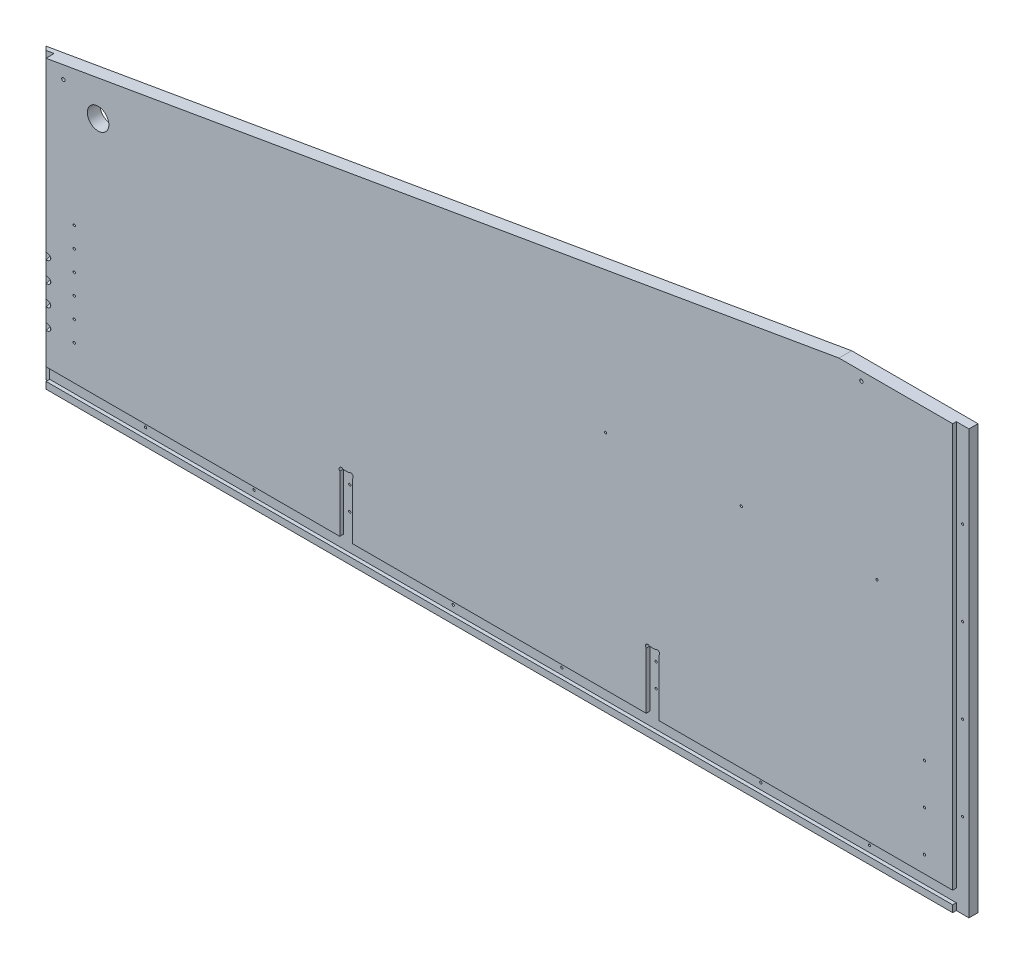
SolidWorks part; units mm, degrees
material "Maple"
ref_plane "Front Plane" through (0, 0, 0) normal (0, 0, 1) x (1, 0, 0)
ref_plane "Top Plane" through (0, 0, 0) normal (0, 1, 0) x (1, 0, 0)
ref_plane "Right Plane" through (0, 0, 0) normal (1, 0, 0) x (0, 0, -1)
sketch "Sketch1" plane through (0, 0, 0) normal (0, 0, 1) x (1, 0, 0)
  line L0 (8932.6508, -5243.5125) -> (10226.1458, -5243.5125)
  line L1 (9086.3208, -4722.0918) -> (10222.9708, -4853.7812)
  line L2 (8914.8708, -6342.0625) -> (10197.5708, -6342.0625)
  line L3 (8914.8708, -5808.6625) -> (10197.5708, -5808.6625)
  line L4 (8919.6333, -5253.0375) -> (10218.2083, -5253.0375)
  line L5 (9134.2633, -4656.1375) -> (9134.2633, -4638.3575)
  line L6 (9091.0833, -4638.3575) -> (9134.2633, -4638.3575)
  line L7 (9091.0833, -4567.2375) -> (9091.0833, -4638.3575)
  line L8 (9134.2633, -4656.1375) -> (9581.3033, -4656.1375)
  line L9 (9091.0833, -4567.2375) -> (9624.4833, -4567.2375)
  line L10 (9581.3033, -4656.1375) -> (9581.3033, -4638.3575)
  line L11 (9581.3033, -4638.3575) -> (9624.4833, -4638.3575)
  line L12 (9624.4833, -4567.2375) -> (9624.4833, -4638.3575)
  line L13 (8932.6508, -5225.7325) -> (9344.9775, -5225.7325)
  line L14 (8932.6508, -5256.2125) -> (8932.6508, -5243.5125)
  line L15 (8911.6958, -5256.2125) -> (8932.6508, -5256.2125)
  line L16 (8914.8708, -4722.0918) -> (9086.3208, -4722.0918)
  line L17 (8911.6958, -4715.5913) -> (8932.6508, -4715.5913)
  line L18 (8914.8708, -6342.0625) -> (8914.8708, -5808.6625)
  line L19 (12082.9917, -4722.0918) -> (10946.3417, -4853.7812)
  line L20 (12236.6617, -5243.5125) -> (10943.1667, -5243.5125)
  line L21 (10951.1042, -5253.0375) -> (12249.6792, -5253.0375)
  line L22 (10838.3917, -5656.2625) -> (11308.2917, -5656.2625)
  line L23 (10838.3917, -5719.7625) -> (11308.2917, -5719.7625)
  line L24 (10838.3917, -5742.5368) -> (11308.2917, -5742.5368)
  line L25 (10806.6417, -6342.0625) -> (11340.0417, -6342.0625)
  line L26 (10803.4667, -6335.7125) -> (11343.2167, -6335.7125)
  line L27 (10803.4667, -6317.9325) -> (11343.2167, -6317.9325)
  line L28 (10943.1667, -5225.7325) -> (11376.4483, -5225.7325)
  line L29 (11506.7292, -4754.5625) -> (10806.6417, -4827.5875)
  line L30 (11506.7292, -4567.2375) -> (11506.7292, -4754.5625)
  line L31 (10806.6417, -4567.2375) -> (10806.6417, -4827.5875)
  line L32 (10806.6417, -4567.2375) -> (11506.7292, -4567.2375)
  line L33 (10235.6708, -6329.3625) -> (10245.1958, -6329.3625)
  line L34 (10245.1958, -6329.3625) -> (10254.7208, -6278.5625)
  line L35 (10302.3458, -6329.3625) -> (10311.8708, -6278.5625)
  line L36 (10302.3458, -6329.3625) -> (10292.8208, -6329.3625)
  line L37 (10245.1958, -5821.3625) -> (10254.7208, -5872.1625)
  line L38 (10235.6708, -5821.3625) -> (10245.1958, -5821.3625)
  line L39 (10292.8208, -5821.3625) -> (10302.3458, -5821.3625)
  line L40 (10302.3458, -5821.3625) -> (10311.8708, -5872.1625)
  line L41 (10235.6708, -5821.3625) -> (10235.6708, -6329.3625)
  line L42 (10254.7208, -5872.1625) -> (10254.7208, -6278.5625)
  line L43 (10311.8708, -5872.1625) -> (10311.8708, -6278.5625)
  line L44 (10292.8208, -5821.3625) -> (10292.8208, -6329.3625)
  line L45 (8932.6508, -5225.7325) -> (8932.6508, -4715.5913)
  line L46 (8911.6958, -4715.5913) -> (8911.6958, -5256.2125)
  line L47 (8914.8708, -5248.275) -> (8914.8708, -4722.0918)
  line L48 (8919.6333, -5253.0375) -> (8914.8708, -5248.275)
  line L49 (8914.8708, -5145.0875) -> (8937.426, -5145.0875)
  line L50 (8914.8708, -5202.2375) -> (8937.426, -5202.2375)
  line L51 (10838.3917, -5656.2625) -> (10838.3917, -5719.7625)
  line L52 (10832.0417, -5736.1868) -> (10856.1717, -5736.1868)
  line L53 (10806.6417, -6342.0625) -> (10806.6417, -5818.7368)
  line L54 (10832.0417, -5649.9125) -> (10856.1717, -5649.9125)
  line L55 (10832.0417, -5726.1125) -> (10856.1717, -5726.1125)
  line L56 (10806.6417, -5818.7368) -> (10833.9015, -5818.7368)
  line L57 (10832.0417, -5806.0442) -> (10851.6815, -5806.0442)
  line L58 (10856.1717, -5801.5541) -> (10856.1717, -5736.1868)
  line L59 (10838.3917, -5814.2467) -> (10838.3917, -5742.5368)
  line L60 (10832.0417, -5806.0442) -> (10832.0417, -5736.1868)
  line L61 (10803.4667, -6317.9325) -> (10803.4667, -6335.7125)
  line L62 (10197.5708, -5808.6625) -> (10197.5708, -6342.0625)
  line L63 (9762.3842, -6348.4125) -> (9762.3842, -5802.3125)
  line L64 (9780.1642, -6348.4125) -> (9762.3842, -6348.4125)
  line L65 (9780.1642, -5802.3125) -> (9780.1642, -6348.4125)
  line L66 (9762.3842, -5802.3125) -> (9780.1642, -5802.3125)
  line L67 (9332.2775, -6348.4125) -> (9332.2775, -5802.3125)
  line L68 (9332.2775, -6348.4125) -> (9350.0575, -6348.4125)
  line L69 (9350.0575, -5802.3125) -> (9350.0575, -6348.4125)
  line L70 (9332.2775, -5802.3125) -> (9350.0575, -5802.3125)
  line L71 (9993.8374, -6061.075) -> (9993.8374, -6045.2418)
  line L72 (9998.5999, -6065.8375) -> (10014.4331, -6065.8375)
  line L73 (9998.5999, -6084.8875) -> (10014.4331, -6084.8875)
  line L74 (9993.8374, -6105.4832) -> (9993.8374, -6089.65)
  line L75 (9974.7874, -6105.4832) -> (9974.7874, -6089.65)
  line L76 (9954.1917, -6084.8875) -> (9970.0249, -6084.8875)
  line L77 (9974.7874, -6061.075) -> (9974.7874, -6045.2418)
  line L78 (9954.1917, -6065.8375) -> (9970.0249, -6065.8375)
  line L79 (10793.9417, -6237.2875) -> (10816.4969, -6237.2875)
  line L80 (10793.9417, -6294.4375) -> (10816.4969, -6294.4375)
  line L81 (10856.1717, -5649.9125) -> (10856.1717, -5726.1125)
  line L82 (10832.0417, -5726.1125) -> (10832.0417, -5649.9125)
  line L83 (10226.1458, -5225.7325) -> (10226.1458, -5243.5125)
  line L84 (10205.1908, -5257.8) -> (10205.1908, -4844.2499)
  line L85 (10230.9083, -4844.2499) -> (10230.9083, -5257.8)
  line L86 (10205.1908, -5257.8) -> (10230.9083, -5257.8)
  line L87 (10205.1908, -4844.2499) -> (10230.9083, -4844.2499)
  line L88 (10946.3417, -5176.8375) -> (10968.8969, -5176.8375)
  line L89 (9349.4676, -5141.9125) -> (9358.2674, -5141.9125)
  line L90 (10946.3417, -5119.6875) -> (10968.8969, -5119.6875)
  line L91 (9929.011, -4660.9635) -> (10066.0807, -4660.9635)
  line L92 (9929.011, -4678.7435) -> (10066.0807, -4678.7435)
  line L93 (10943.1667, -5225.7325) -> (10943.1667, -5243.5125)
  line L94 (10946.3417, -5248.275) -> (10951.1042, -5253.0375)
  line L95 (10946.3417, -5257.8063) -> (10946.3417, -4849.0188)
  line L96 (10964.1217, -5257.8) -> (10964.1217, -4844.2499)
  line L97 (10938.4042, -4844.2499) -> (10938.4042, -5257.8)
  line L98 (10938.4042, -5257.8) -> (10964.1217, -5257.8)
  line L99 (10964.1217, -4844.2499) -> (10938.4042, -4844.2499)
  line L100 (10344.8908, -4560.8875) -> (10369.0208, -4560.8875)
  line L101 (10344.8908, -4560.8875) -> (10369.0208, -4560.8875)
  line L102 (10800.2917, -4560.8875) -> (10824.4217, -4560.8875)
  line L103 (10200.4156, -5119.6875) -> (10222.9708, -5119.6875)
  line L104 (10200.4156, -5176.8375) -> (10222.9708, -5176.8375)
  line L105 (9344.9775, -5146.4026) -> (9344.9775, -5225.7325)
  line L106 (10344.8908, -4560.8875) -> (10344.8908, -4833.9375)
  line L107 (9792.8642, -5225.7325) -> (9792.8642, -5146.4026)
  line L108 (9362.7575, -5225.7325) -> (9775.0842, -5225.7325)
  line L109 (9680.3633, -4761.8396) -> (9680.3633, -4559.9604)
  line L110 (9656.2333, -4559.9604) -> (9680.3633, -4559.9604)
  line L111 (9656.2333, -4761.8396) -> (9680.3633, -4761.8396)
  line L112 (9656.2333, -4761.8396) -> (9656.2333, -4559.9604)
  line L113 (9779.5743, -5141.9125) -> (9788.374, -5141.9125)
  line L114 (10070.5708, -4665.4536) -> (10070.5708, -4674.2534)
  line L115 (9924.5208, -4674.2534) -> (9924.5208, -4665.4536)
  line L116 (12127.4417, -6188.3925) -> (12205.5015, -6188.3925)
  line L117 (12209.9917, -6170.6125) -> (12209.9917, -6183.9024)
  line L118 (9792.8642, -5225.7325) -> (10226.1458, -5225.7325)
  line L119 (9662.5833, -4754.5625) -> (10362.6708, -4827.5875)
  line L120 (9662.5833, -4567.2375) -> (9662.5833, -4754.5625)
  line L121 (10362.6708, -4567.2375) -> (10362.6708, -4827.5875)
  line L122 (9662.5833, -4567.2375) -> (10362.6708, -4567.2375)
  line L123 (10824.4217, -4833.9375) -> (10800.2917, -4833.9375)
  line L124 (10800.2917, -4833.9375) -> (10800.2917, -4560.8875)
  line L125 (10824.4217, -4560.8875) -> (10824.4217, -4833.9375)
  line L126 (10344.8908, -4833.9375) -> (10369.0208, -4833.9375)
  line L127 (10369.0208, -4833.9375) -> (10369.0208, -4560.8875)
  line L128 (10222.9708, -5248.275) -> (10218.2083, -5253.0375)
  line L129 (10222.9708, -5257.8063) -> (10222.9708, -4849.0188)
  line L130 (11734.6544, -5701.375) -> (11739.2301, -5701.375)
  line L131 (9362.7575, -5225.7325) -> (9362.7575, -5146.4026)
  line L132 (9775.0842, -5146.4026) -> (9775.0842, -5225.7325)
  line L133 (11761.3864, -5701.375) -> (11756.8282, -5701.375)
  line L134 (11734.6544, -5693.755) -> (11739.2301, -5693.755)
  line L135 (11761.4039, -5693.755) -> (11756.8282, -5693.755)
  line L136 (11734.6544, -5701.375) -> (11739.2301, -5701.375)
  line L137 (11744.3462, -5721.3024) -> (11744.3462, -5706.4179)
  line L138 (11751.7122, -5721.3024) -> (11751.7122, -5706.4179)
  line L139 (11740.0917, -6170.6125) -> (11740.0917, -6183.9024)
  line L140 (11689.2917, -6188.3925) -> (11822.6417, -6188.3925)
  line L141 (11689.2917, -6348.4093) -> (11689.2917, -6164.2657)
  line L142 (11689.2917, -6164.2657) -> (11746.4417, -6164.2657)
  line L143 (11746.4417, -6164.2657) -> (11746.4417, -6188.3925)
  line L144 (11689.2917, -6164.2657) -> (11746.4417, -6164.2657)
  line L145 (11340.0417, -5818.7368) -> (11340.0417, -6342.0625)
  line L146 (11290.5117, -5726.1125) -> (11314.6417, -5726.1125)
  line L147 (11290.5117, -5649.9125) -> (11290.5117, -5726.1125)
  line L148 (11340.0417, -5818.7368) -> (11312.7818, -5818.7368)
  line L149 (11314.6417, -5806.0442) -> (11295.0018, -5806.0442)
  line L150 (11290.5117, -5801.5541) -> (11290.5117, -5736.1868)
  line L151 (11308.2917, -5814.2467) -> (11308.2917, -5742.5368)
  line L152 (11314.6417, -5806.0442) -> (11314.6417, -5736.1868)
  line L153 (11290.5117, -5736.1868) -> (11314.6417, -5736.1868)
  line L154 (11848.0417, -6267.1325) -> (11962.3417, -6267.1325)
  line L155 (11962.3417, -6267.1325) -> (11962.3417, -6203.6325)
  line L156 (11343.2167, -6317.9325) -> (11343.2167, -6335.7125)
  line L157 (11365.4417, -5656.2625) -> (11365.4417, -5719.7625)
  line L158 (11365.4417, -5656.2625) -> (11479.7417, -5656.2625)
  line L159 (11778.1917, -6071.3937) -> (11802.3217, -6071.3937)
  line L160 (11314.6417, -5726.1125) -> (11314.6417, -5649.9125)
  line L161 (11314.6417, -5649.9125) -> (11290.5117, -5649.9125)
  line L162 (11308.2917, -5719.7625) -> (11308.2917, -5656.2625)
  line L163 (11689.2917, -6348.4093) -> (11713.4217, -6348.4093)
  line L164 (12203.6417, -6164.2657) -> (12260.7917, -6164.2657)
  line L165 (11713.4217, -6348.4093) -> (11713.4217, -6164.2657)
  line L166 (11695.6417, -6342.0625) -> (11695.6417, -6170.6125)
  line L167 (11695.6417, -6048.5337) -> (11699.4517, -6052.3437)
  line L168 (11822.6417, -6292.5325) -> (11822.6417, -6188.3925)
  line L169 (11695.6417, -6342.0625) -> (11695.6417, -6170.6125)
  line L170 (11848.0417, -6203.6325) -> (11962.3417, -6203.6325)
  line L171 (11848.0417, -6203.6325) -> (11848.0417, -6267.1325)
  line L172 (11987.7417, -6267.1325) -> (11987.7417, -6203.6325)
  line L173 (11784.5417, -6077.7437) -> (11784.5417, -6141.2438)
  line L174 (11517.8417, -5656.2625) -> (11632.1417, -5656.2625)
  line L175 (11632.1417, -5656.2625) -> (11632.1417, -5719.7625)
  line L176 (11632.1417, -5719.7625) -> (11517.8417, -5719.7625)
  line L177 (11517.8417, -5719.7625) -> (11517.8417, -5656.2625)
  line L178 (11692.4667, -6028.2137) -> (11692.4667, -6045.9937)
  line L179 (11695.6417, -5979.3188) -> (11718.1969, -5979.3188)
  line L180 (11695.6417, -5922.1687) -> (11718.1969, -5922.1687)
  line L181 (11821.0415, -5722.9375) -> (11821.0415, -5943.6)
  line L182 (11687.7042, -5651.5) -> (11701.9917, -5651.5)
  line L183 (11687.7042, -5651.5) -> (11687.7042, -6055.5251)
  line L184 (11687.7042, -6055.5251) -> (11701.9917, -6055.5251)
  line L185 (11701.9917, -6055.5251) -> (11701.9917, -5651.5)
  line L186 (11695.6417, -6055.2013) -> (11695.6417, -5649.595)
  line L187 (11695.6417, -5656.2625) -> (11695.6417, -6048.5337)
  line L188 (11695.6417, -6170.6125) -> (11740.0917, -6170.6125)
  line L189 (12203.6417, -6164.2657) -> (12203.6417, -6188.3925)
  line L190 (12254.4417, -6342.0625) -> (12254.4417, -6170.6125)
  line L191 (12129.0419, -5943.6) -> (12129.0419, -5722.9375)
  line L192 (12254.4417, -6048.5337) -> (12250.6317, -6052.3437)
  line L193 (12257.6167, -6045.9937) -> (12257.6167, -6028.2137)
  line L194 (12248.0917, -5651.5) -> (12262.3792, -5651.5)
  line L195 (12262.3792, -5651.5) -> (12262.3792, -6055.5251)
  line L196 (12262.3792, -6055.5251) -> (12248.0917, -6055.5251)
  line L197 (12248.0917, -6055.5251) -> (12248.0917, -5651.5)
  line L198 (12254.4417, -6141.2438) -> (12254.4417, -6077.7437)
  line L199 (12236.6617, -6164.2657) -> (12260.7917, -6164.2657)
  line L200 (12102.0417, -6267.1325) -> (11987.7417, -6267.1325)
  line L201 (11330.1865, -6237.2875) -> (11352.7417, -6237.2875)
  line L202 (11330.1865, -6294.4375) -> (11352.7417, -6294.4375)
  line L203 (11474.6617, -5851.8425) -> (11492.4417, -5851.8425)
  line L204 (11474.6617, -5808.6625) -> (11474.6617, -5851.8425)
  line L205 (11403.5417, -5808.6625) -> (11474.6617, -5808.6625)
  line L206 (11492.4417, -5851.8425) -> (11492.4417, -6298.8825)
  line L207 (11403.5417, -6342.0625) -> (11403.5417, -5808.6625)
  line L208 (11474.6617, -6298.8825) -> (11492.4417, -6298.8825)
  line L209 (11474.6617, -6342.0625) -> (11474.6617, -6298.8825)
  line L210 (11403.5417, -6342.0625) -> (11474.6617, -6342.0625)
  line L211 (11619.4417, -5851.8425) -> (11601.6617, -5851.8425)
  line L212 (11601.6617, -5808.6625) -> (11601.6617, -5851.8425)
  line L213 (11530.5417, -5808.6625) -> (11601.6617, -5808.6625)
  line L214 (11619.4417, -5851.8425) -> (11619.4417, -6298.8825)
  line L215 (11530.5417, -6342.0625) -> (11530.5417, -5808.6625)
  line L216 (11619.4417, -6298.8825) -> (11601.6617, -6298.8825)
  line L217 (11601.6617, -6342.0625) -> (11601.6617, -6298.8825)
  line L218 (11530.5417, -6342.0625) -> (11601.6617, -6342.0625)
  line L219 (11479.7417, -5719.7625) -> (11479.7417, -5656.2625)
  line L220 (11365.4417, -5719.7625) -> (11479.7417, -5719.7625)
  line L221 (11778.1917, -6147.5937) -> (11802.3217, -6147.5937)
  line L222 (11802.3217, -6071.3937) -> (11802.3217, -6147.5937)
  line L223 (11778.1917, -6147.5937) -> (11778.1917, -6071.3937)
  line L224 (12254.4417, -5922.1687) -> (12231.8865, -5922.1687)
  line L225 (12254.4417, -5979.3188) -> (12231.8865, -5979.3188)
  line L226 (12254.4417, -6055.2013) -> (12254.4417, -5649.595)
  line L227 (12254.4417, -6048.5337) -> (12254.4417, -5656.2625)
  line L228 (11841.6917, -5702.2873) -> (12108.3917, -5702.2873)
  line L229 (11822.6417, -6292.5325) -> (12127.4417, -6292.5325)
  line L230 (12127.4417, -6292.5325) -> (12127.4417, -6188.3925)
  line L231 (12254.4417, -6170.6125) -> (12209.9917, -6170.6125)
  line L232 (11695.6417, -6342.0625) -> (12254.4417, -6342.0625)
  line L233 (12236.6617, -6348.4093) -> (12260.7917, -6348.4093)
  line L234 (12260.7917, -6348.4093) -> (12260.7917, -6164.2657)
  line L235 (12236.6617, -6348.4093) -> (12236.6617, -6164.2657)
  line L236 (12102.0417, -6203.6325) -> (12102.0417, -6267.1325)
  line L237 (11987.7417, -6203.6325) -> (12102.0417, -6203.6325)
  line L238 (12236.6617, -6147.5937) -> (12236.6617, -6071.3937)
  line L239 (12203.6417, -6188.3925) -> (12260.7917, -6188.3925)
  line L240 (11098.7417, -4665.4536) -> (11098.7417, -4674.2534)
  line L241 (11394.2283, -5146.4026) -> (11394.2283, -5225.7325)
  line L242 (11376.4483, -5225.7325) -> (11376.4483, -5146.4026)
  line L243 (11394.2283, -5225.7325) -> (11806.555, -5225.7325)
  line L244 (11841.6917, -5964.2502) -> (12108.3917, -5964.2502)
  line L245 (12236.6617, -6147.5937) -> (12260.7917, -6147.5937)
  line L246 (12236.6617, -5256.2125) -> (12236.6617, -5243.5125)
  line L247 (12260.7917, -6147.5937) -> (12260.7917, -6071.3937)
  line L248 (12260.7917, -6071.3937) -> (12236.6617, -6071.3937)
  line L249 (12254.4417, -6077.7437) -> (11784.5417, -6077.7437)
  line L250 (11784.5417, -6141.2438) -> (12254.4417, -6141.2438)
  line L252 (12254.4417, -5656.2625) -> (11695.6417, -5656.2625)
  line L253 (11699.4517, -6052.3437) -> (12250.6317, -6052.3437)
  line L254 (11692.4667, -6045.9937) -> (12257.6167, -6045.9937)
  line L255 (11692.4667, -6028.2137) -> (12257.6167, -6028.2137)
  line L256 (11824.335, -5146.4026) -> (11824.335, -5225.7325)
  line L257 (11811.0451, -5141.9125) -> (11819.8449, -5141.9125)
  line L258 (11244.7917, -4674.2534) -> (11244.7917, -4665.4536)
  line L259 (11806.555, -5225.7325) -> (11806.555, -5146.4026)
  line L260 (11488.9492, -4761.8396) -> (11488.9492, -4559.9604)
  line L261 (11488.9492, -4559.9604) -> (11513.0792, -4559.9604)
  line L262 (11488.9492, -4761.8396) -> (11513.0792, -4761.8396)
  line L263 (11513.0792, -4761.8396) -> (11513.0792, -4559.9604)
  line L264 (11240.3015, -4660.9635) -> (11103.2318, -4660.9635)
  line L265 (11103.2318, -4678.7435) -> (11240.3015, -4678.7435)
  line L266 (12236.6617, -5225.7325) -> (12236.6617, -4715.5913)
  line L267 (12257.6167, -4715.5913) -> (12257.6167, -5256.2125)
  line L268 (12254.4417, -5248.275) -> (12254.4417, -4722.0918)
  line L269 (12236.6617, -5225.7325) -> (11824.335, -5225.7325)
  line L270 (12035.0492, -4656.1375) -> (12035.0492, -4638.3575)
  line L271 (12078.2292, -4638.3575) -> (12035.0492, -4638.3575)
  line L272 (12078.2292, -4567.2375) -> (12078.2292, -4638.3575)
  line L273 (12035.0492, -4656.1375) -> (11588.0092, -4656.1375)
  line L274 (11544.8292, -4567.2375) -> (12078.2292, -4567.2375)
  line L275 (11588.0092, -4656.1375) -> (11588.0092, -4638.3575)
  line L276 (11544.8292, -4638.3575) -> (11588.0092, -4638.3575)
  line L277 (11544.8292, -4567.2375) -> (11544.8292, -4638.3575)
  line L278 (12249.6792, -5253.0375) -> (12254.4417, -5248.275)
  line L280 (12257.6167, -5256.2125) -> (12236.6617, -5256.2125)
  line L281 (12231.8865, -5145.0875) -> (12254.4417, -5145.0875)
  line L282 (12231.8865, -5202.2375) -> (12254.4417, -5202.2375)
  line L283 (12236.6617, -4715.5913) -> (12257.6167, -4715.5913)
  line L284 (12082.9917, -4722.0918) -> (12254.4417, -4722.0918)
  line L285 (11380.9385, -5141.9125) -> (11389.7382, -5141.9125)
  circle A0 centre (8923.7608, -4778.9042) radius 1.5875
  circle A1 centre (9062.6598, -4736.3765) radius 2.3685
  circle A2 centre (9051.3958, -6281.7375) radius 22.225
  circle A3 centre (9083.1458, -6249.9875) radius 1.5875
  circle A4 centre (9083.1458, -6313.4875) radius 1.5875
  circle A5 centre (9019.6458, -6249.9875) radius 1.5875
  circle A6 centre (9019.6458, -6313.4875) radius 1.5875
  circle A7 centre (8972.3383, -5202.2375) radius 1.5875
  circle A8 centre (8923.7608, -5015.9708) radius 1.5875
  circle A9 centre (8923.7608, -5134.5042) radius 1.5875
  circle A10 centre (9054.5708, -5234.6225) radius 1.5875
  circle A11 centre (8923.7608, -4897.4375) radius 1.5875
  circle A12 centre (8972.3383, -5087.9375) radius 1.5875
  circle A13 centre (8972.3383, -5145.0875) radius 1.5875
  circle A14 centre (10847.2817, -5668.9625) radius 1.5875
  circle A15 centre (10847.2817, -5707.0625) radius 1.5875
  circle A16 centre (10847.2817, -5755.2368) radius 1.5875
  circle A17 centre (10851.4092, -6237.2875) radius 1.5875
  circle A18 centre (10851.4092, -6294.4375) radius 1.5875
  circle A19 centre (10847.2817, -5793.3442) radius 1.5875
  arc A20 (10833.9015, -5818.7368) -> (10838.3917, -5814.2467) centre (10836.1466, -5816.4918) ccw
  arc A21 (10851.6815, -5806.0442) -> (10856.1717, -5801.5541) centre (10853.9266, -5803.7992) ccw
  circle A22 centre (10882.8417, -6040.4375) radius 1.5875
  circle A23 centre (10882.8417, -6218.2375) radius 1.5875
  circle A24 centre (10882.8417, -5862.6375) radius 1.5875
  circle A25 centre (10908.2417, -6326.8225) radius 1.5875
  circle A26 centre (10908.2417, -6326.8225) radius 1.5875
  circle A27 centre (10851.4092, -6180.1375) radius 1.5875
  circle A28 centre (10815.5317, -4783.4231) radius 1.5875
  circle A29 centre (10815.5317, -4696.9488) radius 1.5875
  circle A30 centre (10815.5317, -4610.4746) radius 1.5875
  circle A31 centre (10979.1323, -4867.0082) radius 2.3685
  circle A32 centre (10190.1802, -4867.0082) radius 2.3685
  circle A33 centre (10955.2317, -4929.9812) radius 1.5875
  circle A34 centre (10955.2317, -5031.5812) radius 1.5875
  circle A35 centre (10214.0808, -4929.9812) radius 1.5875
  circle A36 centre (10214.0808, -5031.5812) radius 1.5875
  circle A37 centre (9341.1675, -6265.8625) radius 1.5875
  circle A38 centre (9771.2742, -5884.8625) radius 1.5875
  circle A39 centre (9771.2742, -6138.8625) radius 1.5875
  circle A40 centre (9771.2742, -6011.8625) radius 1.5875
  arc A41 (10036.2287, -6113.8083) -> (10051.3426, -6111.6033) centre (10042.9639, -6107.0732) ccw
  arc A42 (10051.3426, -6111.6033) -> (10051.3426, -6039.1217) centre (9984.3124, -6075.3625) ccw
  arc A43 (10051.3426, -6039.1217) -> (10036.2287, -6036.9167) centre (10042.9639, -6043.6518) ccw
  arc A44 (10034.5851, -6102.5431) -> (10034.5851, -6048.1819) centre (9984.3124, -6075.3625) ccw
  arc A45 (10034.5851, -6102.5431) -> (10036.2287, -6113.8083) centre (10042.9639, -6107.0732) ccw
  arc A46 (10036.2287, -6036.9167) -> (10034.5851, -6048.1819) centre (10042.9639, -6043.6518) ccw
  arc A47 (9945.8666, -6127.2787) -> (9948.0717, -6142.3927) centre (9952.6018, -6134.0139) ccw
  arc A48 (9948.0717, -6142.3927) -> (10020.5532, -6142.3927) centre (9984.3124, -6075.3625) ccw
  arc A49 (10020.5532, -6142.3927) -> (10022.7583, -6127.2787) centre (10016.0231, -6134.0139) ccw
  arc A50 (9957.1319, -6125.6352) -> (10011.493, -6125.6352) centre (9984.3124, -6075.3625) ccw
  arc A51 (9957.1319, -6125.6352) -> (9945.8666, -6127.2787) centre (9952.6018, -6134.0139) ccw
  arc A52 (10022.7583, -6127.2787) -> (10011.493, -6125.6352) centre (10016.0231, -6134.0139) ccw
  arc A53 (9932.3962, -6036.9167) -> (9917.2822, -6039.1217) centre (9925.661, -6043.6518) ccw
  arc A54 (9917.2822, -6039.1217) -> (9917.2822, -6111.6033) centre (9984.3124, -6075.3625) ccw
  arc A55 (9917.2822, -6111.6033) -> (9932.3962, -6113.8083) centre (9925.661, -6107.0732) ccw
  arc A56 (9934.0398, -6048.1819) -> (9934.0398, -6102.5431) centre (9984.3124, -6075.3625) ccw
  arc A57 (9934.0398, -6048.1819) -> (9932.3962, -6036.9167) centre (9925.661, -6043.6518) ccw
  arc A58 (9932.3962, -6113.8083) -> (9934.0398, -6102.5431) centre (9925.661, -6107.0732) ccw
  arc A59 (9945.8666, -6023.4463) -> (9957.1319, -6025.0898) centre (9952.6018, -6016.7111) ccw
  arc A60 (10011.493, -6025.0898) -> (10022.7583, -6023.4463) centre (10016.0231, -6016.7111) ccw
  arc A61 (10011.493, -6025.0898) -> (9957.1319, -6025.0898) centre (9984.3124, -6075.3625) ccw
  arc A62 (9948.0717, -6008.3323) -> (9945.8666, -6023.4463) centre (9952.6018, -6016.7111) ccw
  arc A63 (10020.5532, -6008.3323) -> (9948.0717, -6008.3323) centre (9984.3124, -6075.3625) ccw
  arc A64 (10022.7583, -6023.4463) -> (10020.5532, -6008.3323) centre (10016.0231, -6016.7111) ccw
  arc A65 (10005.0943, -6187.7574) -> (10096.7073, -6096.1443) centre (9984.3124, -6075.3625) ccw
  arc A66 (9993.8374, -6178.3911) -> (10005.0943, -6187.7574) centre (10003.3624, -6178.3911) ccw
  arc A67 (10001.6306, -6169.0249) -> (10077.9748, -6092.6807) centre (9984.3124, -6075.3625) ccw
  arc A68 (10087.3411, -6084.8875) -> (10077.9748, -6092.6807) centre (10087.3411, -6094.4125) ccw
  arc A69 (10001.6306, -6169.0249) -> (9993.8374, -6178.3911) centre (10003.3624, -6178.3911) ccw
  arc A70 (9963.5306, -6187.7574) -> (9974.7874, -6178.3911) centre (9965.2624, -6178.3911) ccw
  arc A71 (9871.9176, -6096.1443) -> (9963.5306, -6187.7574) centre (9984.3124, -6075.3625) ccw
  arc A72 (9881.2838, -6084.8875) -> (9871.9176, -6096.1443) centre (9881.2838, -6094.4125) ccw
  arc A73 (9890.65, -6092.6807) -> (9966.9943, -6169.0249) centre (9984.3124, -6075.3625) ccw
  arc A74 (9974.7874, -6178.3911) -> (9966.9943, -6169.0249) centre (9965.2624, -6178.3911) ccw
  arc A75 (9890.65, -6092.6807) -> (9881.2838, -6084.8875) centre (9881.2838, -6094.4125) ccw
  arc A76 (9871.9176, -6054.5807) -> (9881.2838, -6065.8375) centre (9881.2838, -6056.3125) ccw
  arc A77 (9963.5306, -5962.9676) -> (9871.9176, -6054.5807) centre (9984.3124, -6075.3625) ccw
  arc A78 (9974.7874, -5972.3339) -> (9963.5306, -5962.9676) centre (9965.2624, -5972.3339) ccw
  arc A79 (9966.9943, -5981.7001) -> (9890.65, -6058.0443) centre (9984.3124, -6075.3625) ccw
  arc A80 (9881.2838, -6065.8375) -> (9890.65, -6058.0443) centre (9881.2838, -6056.3125) ccw
  arc A81 (9966.9943, -5981.7001) -> (9974.7874, -5972.3339) centre (9965.2624, -5972.3339) ccw
  arc A82 (10077.9748, -6058.0443) -> (10087.3411, -6065.8375) centre (10087.3411, -6056.3125) ccw
  arc A83 (9993.8374, -5972.3339) -> (10001.6306, -5981.7001) centre (10003.3624, -5972.3339) ccw
  arc A84 (10077.9748, -6058.0443) -> (10001.6306, -5981.7001) centre (9984.3124, -6075.3625) ccw
  arc A85 (10087.3411, -6065.8375) -> (10096.7073, -6054.5807) centre (10087.3411, -6056.3125) ccw
  arc A86 (10096.7073, -6054.5807) -> (10005.0943, -5962.9676) centre (9984.3124, -6075.3625) ccw
  arc A87 (10005.0943, -5962.9676) -> (9993.8374, -5972.3339) centre (10003.3624, -5972.3339) ccw
  arc A88 (10014.4331, -6065.8375) -> (10018.7361, -6059.0339) centre (10014.4331, -6061.075) ccw
  arc A89 (10018.7361, -6059.0339) -> (10000.641, -6040.9388) centre (9984.3124, -6075.3625) ccw
  arc A90 (10000.641, -6040.9388) -> (9993.8374, -6045.2418) centre (9998.5999, -6045.2418) ccw
  arc A91 (9993.8374, -6061.075) -> (9998.5999, -6065.8375) centre (9998.5999, -6061.075) ccw
  arc A92 (9993.8374, -6105.4832) -> (10000.641, -6109.7862) centre (9998.5999, -6105.4832) ccw
  arc A93 (10000.641, -6109.7862) -> (10018.7361, -6091.6911) centre (9984.3124, -6075.3625) ccw
  arc A94 (10018.7361, -6091.6911) -> (10014.4331, -6084.8875) centre (10014.4331, -6089.65) ccw
  arc A95 (9998.5999, -6084.8875) -> (9993.8374, -6089.65) centre (9998.5999, -6089.65) ccw
  arc A96 (9954.1917, -6084.8875) -> (9949.8888, -6091.6911) centre (9954.1917, -6089.65) ccw
  arc A97 (9949.8888, -6091.6911) -> (9967.9839, -6109.7862) centre (9984.3124, -6075.3625) ccw
  arc A98 (9967.9839, -6109.7862) -> (9974.7874, -6105.4832) centre (9970.0249, -6105.4832) ccw
  arc A99 (9974.7874, -6089.65) -> (9970.0249, -6084.8875) centre (9970.0249, -6089.65) ccw
  arc A100 (9970.0249, -6065.8375) -> (9974.7874, -6061.075) centre (9970.0249, -6061.075) ccw
  arc A101 (9949.8888, -6059.0339) -> (9954.1917, -6065.8375) centre (9954.1917, -6061.075) ccw
  arc A102 (9967.9839, -6040.9388) -> (9949.8888, -6059.0339) centre (9984.3124, -6075.3625) ccw
  arc A103 (9974.7874, -6045.2418) -> (9967.9839, -6040.9388) centre (9970.0249, -6045.2418) ccw
  arc A104 (10096.7073, -6096.1443) -> (10087.3411, -6084.8875) centre (10087.3411, -6094.4125) ccw
  circle A105 centre (9771.2742, -6265.8625) radius 1.5875
  circle A106 centre (9341.1675, -5884.8625) radius 1.5875
  circle A107 centre (9341.1675, -6138.8625) radius 1.5875
  circle A108 centre (9341.1675, -6011.8625) radius 1.5875
  circle A109 centre (11037.2315, -4887.5494) radius 15.0812
  arc A110 (9349.4676, -5141.9125) -> (9344.9775, -5146.4026) centre (9347.2226, -5144.1576) ccw
  arc A111 (9362.7575, -5146.4026) -> (9358.2674, -5141.9125) centre (9360.5124, -5144.1576) ccw
  circle A112 centre (9946.7458, -4669.8535) radius 1.5875
  arc A113 (9924.5208, -4674.2534) -> (9929.011, -4678.7435) centre (9926.7659, -4676.4984) ccw
  circle A114 centre (11003.8092, -5176.8375) radius 1.5875
  circle A115 centre (11003.8092, -5119.6875) radius 1.5875
  circle A116 centre (10353.7808, -4696.9488) radius 1.5875
  circle A117 centre (10353.7808, -4610.4746) radius 1.5875
  circle A118 centre (10353.7808, -4783.4231) radius 1.5875
  circle A119 centre (11003.8092, -5062.5375) radius 1.5875
  circle A120 centre (9353.8675, -5160.9625) radius 1.5875
  circle A121 centre (9638.7708, -5234.6225) radius 1.5875
  circle A122 centre (9671.4733, -4724.1144) radius 1.5875
  circle A123 centre (9671.4733, -4661.3637) radius 1.5875
  circle A124 centre (9671.4733, -4598.6129) radius 1.5875
  arc A125 (9792.8642, -5146.4026) -> (9788.374, -5141.9125) centre (9790.6191, -5144.1576) ccw
  arc A126 (9779.5743, -5141.9125) -> (9775.0842, -5146.4026) centre (9777.3292, -5144.1576) ccw
  circle A127 centre (10048.3458, -4669.8535) radius 1.5875
  arc A128 (10070.5708, -4665.4536) -> (10066.0807, -4660.9635) centre (10068.3258, -4663.2086) ccw
  arc A129 (10066.0807, -4678.7435) -> (10070.5708, -4674.2534) centre (10068.3258, -4676.4984) ccw
  circle A130 centre (9997.5458, -4669.8535) radius 1.5875
  arc A131 (9929.011, -4660.9635) -> (9924.5208, -4665.4536) centre (9926.7659, -4663.2086) ccw
  circle A132 centre (10132.081, -4887.5494) radius 15.0812
  circle A133 centre (10165.5033, -5176.8375) radius 1.5875
  circle A134 centre (10165.5033, -5119.6875) radius 1.5875
  circle A135 centre (9486.3708, -5234.6225) radius 1.5875
  circle A136 centre (10165.5033, -5062.5375) radius 1.5875
  circle A137 centre (9206.9708, -5234.6225) radius 1.5875
  circle A138 centre (10070.5708, -5234.6225) radius 1.5875
  circle A139 centre (9918.1708, -5234.6225) radius 1.5875
  circle A140 centre (9783.9742, -5160.9625) radius 1.5875
  circle A141 centre (9783.9742, -5193.9825) radius 1.5875
  circle A142 centre (9353.8675, -5193.9825) radius 1.5875
  circle A143 centre (11073.3417, -6326.8225) radius 1.5875
  circle A144 centre (11073.3417, -6326.8225) radius 1.5875
  circle A145 centre (11295.2742, -6180.1375) radius 1.5875
  circle A146 centre (11295.2742, -6294.4375) radius 1.5875
  circle A147 centre (11295.2742, -6237.2875) radius 1.5875
  circle A148 centre (11975.0417, -5692.775) radius 3.4925
  circle A149 centre (11263.8417, -5862.6375) radius 1.5875
  arc A150 (11739.2301, -5701.375) -> (11744.3462, -5706.4179) centre (11748.0292, -5697.565) ccw
  arc A151 (11751.7122, -5706.4179) -> (11756.8282, -5701.375) centre (11748.0292, -5697.565) ccw
  arc A152 (11744.3462, -5721.3024) -> (11751.7122, -5721.3024) centre (11748.0292, -5725.505) ccw
  arc A153 (11734.6544, -5693.755) -> (11724.9787, -5697.565) centre (11730.5667, -5697.565) ccw
  arc A154 (11756.8282, -5693.755) -> (11739.2301, -5693.755) centre (11748.0292, -5697.565) ccw
  arc A155 (11724.9787, -5697.565) -> (11734.6544, -5701.375) centre (11730.5667, -5697.565) ccw
  arc A156 (11761.3864, -5701.375) -> (11771.0797, -5697.565) centre (11765.4842, -5697.565) ccw
  arc A157 (11771.0797, -5697.565) -> (11761.4039, -5693.755) centre (11765.4917, -5697.565) ccw
  arc A158 (11740.0917, -6183.9024) -> (11744.5818, -6188.3925) centre (11742.3367, -6186.1474) ccw
  arc A159 (12205.5015, -6188.3925) -> (12209.9917, -6183.9024) centre (12207.7466, -6186.1474) ccw
  circle A160 centre (11299.4017, -5793.3442) radius 1.5875
  arc A161 (11308.2917, -5814.2467) -> (11312.7818, -5818.7368) centre (11310.5367, -5816.4918) ccw
  arc A162 (11290.5117, -5801.5541) -> (11295.0018, -5806.0442) centre (11292.7567, -5803.7992) ccw
  circle A163 centre (11704.5317, -6314.149) radius 1.5875
  circle A164 centre (11748.9817, -6208.7125) radius 1.5875
  circle A165 centre (11263.8417, -6218.2375) radius 1.5875
  circle A166 centre (11263.8417, -6040.4375) radius 1.5875
  circle A167 centre (11238.4417, -6326.8225) radius 1.5875
  circle A168 centre (11238.4417, -6326.8225) radius 1.5875
  circle A169 centre (11299.4017, -5668.9625) radius 1.5875
  circle A170 centre (11299.4017, -5707.0625) radius 1.5875
  circle A171 centre (11726.7567, -6179.5025) radius 1.5875
  circle A172 centre (11704.5317, -6199.3198) radius 1.5875
  circle A173 centre (11748.9817, -6272.2125) radius 1.5875
  circle A174 centre (11704.5317, -6256.7344) radius 1.5875
  circle A175 centre (11299.4017, -5755.2368) radius 1.5875
  circle A176 centre (11913.4467, -6301.4225) radius 1.5875
  circle A177 centre (11790.2567, -6301.4225) radius 1.5875
  circle A178 centre (11793.4317, -6128.5437) radius 1.5875
  circle A179 centre (11753.1092, -5865.0188) radius 1.5875
  circle A180 centre (11809.9417, -6037.1038) radius 1.5875
  circle A181 centre (11809.9417, -6037.1038) radius 1.5875
  circle A182 centre (11753.1092, -5922.1687) radius 1.5875
  circle A183 centre (11975.0417, -5973.7625) radius 3.4925
  circle A184 centre (11975.0417, -6037.1038) radius 1.5875
  circle A185 centre (11753.1092, -5979.3188) radius 1.5875
  circle A186 centre (11975.0417, -6037.1038) radius 1.5875
  arc A187 (11841.6917, -5702.2873) -> (11821.0415, -5722.9375) centre (11841.6917, -5722.9375) ccw
  circle A188 centre (11811.5292, -5833.2687) radius 3.4925
  arc A189 (11821.0415, -5943.6) -> (11841.6917, -5964.2502) centre (11841.6917, -5943.6) ccw
  circle A190 centre (12196.9742, -5865.0188) radius 1.5875
  arc A191 (12129.0419, -5722.9375) -> (12108.3917, -5702.2873) centre (12108.3917, -5722.9375) ccw
  circle A192 centre (12036.6367, -6301.4225) radius 1.5875
  circle A193 centre (12159.8267, -6301.4225) radius 1.5875
  circle A194 centre (12138.5542, -5833.2687) radius 3.4925
  circle A195 centre (12197.2917, -5761.0375) radius 15.0812
  circle A196 centre (11793.4317, -6090.4437) radius 1.5875
  circle A197 centre (12196.9742, -5922.1687) radius 1.5875
  arc A198 (12108.3917, -5964.2502) -> (12129.0419, -5943.6) centre (12108.3917, -5943.6) ccw
  circle A199 centre (12196.9742, -5979.3188) radius 1.5875
  circle A200 centre (12201.1017, -6272.2125) radius 1.5875
  circle A201 centre (12245.5517, -6314.149) radius 1.5875
  circle A202 centre (12245.5517, -6256.7344) radius 1.5875
  circle A203 centre (12201.1017, -6208.7125) radius 1.5875
  circle A204 centre (12223.3267, -6179.5025) radius 1.5875
  circle A205 centre (12245.5517, -6199.3198) radius 1.5875
  circle A206 centre (11171.7667, -4669.8535) radius 1.5875
  circle A207 centre (11222.5667, -4669.8535) radius 1.5875
  arc A208 (11240.3015, -4678.7435) -> (11244.7917, -4674.2534) centre (11242.5466, -4676.4984) ccw
  circle A209 centre (11385.3383, -5193.9825) radius 1.5875
  circle A210 centre (12106.6527, -4736.3765) radius 2.3685
  circle A211 centre (12140.1417, -6037.1038) radius 1.5875
  circle A212 centre (12140.1417, -6037.1038) radius 1.5875
  circle A213 centre (12245.5517, -6090.4437) radius 1.5875
  circle A214 centre (12245.5517, -6128.5437) radius 1.5875
  circle A215 centre (11385.3383, -5160.9625) radius 1.5875
  arc A216 (11824.335, -5146.4026) -> (11819.8449, -5141.9125) centre (11822.0899, -5144.1576) ccw
  arc A217 (11811.0451, -5141.9125) -> (11806.555, -5146.4026) centre (11808.8001, -5144.1576) ccw
  circle A218 centre (11815.445, -5193.9825) radius 1.5875
  circle A219 centre (11815.445, -5160.9625) radius 1.5875
  circle A220 centre (11530.5417, -5234.6225) radius 1.5875
  circle A221 centre (11962.3417, -5234.6225) radius 1.5875
  arc A222 (11244.7917, -4665.4536) -> (11240.3015, -4660.9635) centre (11242.5466, -4663.2086) ccw
  circle A223 centre (11682.9417, -5234.6225) radius 1.5875
  circle A224 centre (11497.8392, -4724.1144) radius 1.5875
  circle A225 centre (11497.8392, -4661.3637) radius 1.5875
  circle A226 centre (11497.8392, -4598.6129) radius 1.5875
  circle A227 centre (11120.9667, -4669.8535) radius 1.5875
  arc A228 (11103.2318, -4660.9635) -> (11098.7417, -4665.4536) centre (11100.9867, -4663.2086) ccw
  arc A229 (11098.7417, -4674.2534) -> (11103.2318, -4678.7435) centre (11100.9867, -4676.4984) ccw
  circle A230 centre (12196.9742, -5202.2375) radius 1.5875
  circle A231 centre (12245.5517, -5015.9708) radius 1.5875
  circle A232 centre (12245.5517, -5134.5042) radius 1.5875
  circle A233 centre (12114.7417, -5234.6225) radius 1.5875
  circle A234 centre (12245.5517, -4897.4375) radius 1.5875
  circle A235 centre (12245.5517, -4778.9042) radius 1.5875
  circle A236 centre (12196.9742, -5087.9375) radius 1.5875
  circle A237 centre (12196.9742, -5145.0875) radius 1.5875
  circle A238 centre (11098.7417, -5234.6225) radius 1.5875
  circle A239 centre (11251.1417, -5234.6225) radius 1.5875
  arc A240 (11380.9385, -5141.9125) -> (11376.4483, -5146.4026) centre (11378.6934, -5144.1576) ccw
  arc A241 (11394.2283, -5146.4026) -> (11389.7382, -5141.9125) centre (11391.9833, -5144.1576) ccw
sketch "CabSideLeft_Outline" plane through (0, 0, 0) normal (0, 0, 1) x (1, 0, 0)
  line L0 (10946.3417, -4853.7812) -> (10946.3417, -5253.0375)
  line L2 (10946.3417, -5253.0375) -> (12254.4417, -5253.0375)
  line L4 (12254.4417, -5253.0375) -> (12254.4417, -4658.6775)
  line L5 (12254.4417, -4658.6775) -> (12077.078, -4658.6775)
  line L8 (12077.078, -4658.6775) -> (10946.3417, -4853.7812)
  dimension "CabSideLeft_Length" = 1308.1
  dimension "CabSideLeft_Front" = 399.2562
  dimension "CabSideLeft_BackHeight" = 594.36
  dimension "CabSideLeft_SlopeLength" = 1147.445
extrude "CabSideLeft_Thickness" add sketch "CabSideLeft_Outline" against normal blind 17.78
sketch "CabSideLeft_LedgeCuts" plane through (0, 0, 0) normal (0, 0, 1) x (1, 0, 0)
  line L0 (10946.3417, -5225.7325) -> (10946.3417, -5243.5125)
  line L1 (10946.3417, -5243.5125) -> (12236.6617, -5243.5125)
  line L2 (12236.6617, -5243.5125) -> (12236.6617, -5253.0375)
  line L3 (12236.6617, -5253.0375) -> (12254.4417, -5253.0375)
  line L4 (12254.4417, -5253.0375) -> (12254.4417, -4658.6775)
  line L5 (12254.4417, -4658.6775) -> (12236.6617, -4658.6775)
  line L6 (12236.6617, -4658.6775) -> (12236.6617, -5225.7325)
  line L7 (12236.6617, -5225.7325) -> (11824.335, -5225.7325)
  line L8 (11824.335, -5225.7325) -> (11824.335, -5141.9125)
  line L9 (11824.335, -5141.9125) -> (11806.555, -5141.9125)
  line L10 (11806.555, -5141.9125) -> (11806.555, -5225.7325)
  line L11 (11806.555, -5225.7325) -> (11394.2283, -5225.7325)
  line L12 (11394.2283, -5225.7325) -> (11394.2283, -5141.9125)
  line L13 (11394.2283, -5141.9125) -> (11376.4483, -5141.9125)
  line L14 (11376.4483, -5141.9125) -> (11376.4483, -5225.7325)
  line L15 (11376.4483, -5225.7325) -> (10946.3417, -5225.7325)
  line L17 (10946.3417, -5253.0375) -> (12254.4417, -5253.0375) construction
  line L18 (10946.3417, -4853.7812) -> (10946.3417, -5253.0375) construction
  line L19 (12254.4417, -4658.6775) -> (12077.078, -4658.6775) construction
  line L20 (12254.4417, -5253.0375) -> (12254.4417, -4658.6775) construction
  dimension "BottomThickness" = 17.78
  dimension "BraceThickness_1" = 17.78
  dimension "BraceThickness_2" = 17.78
  dimension "BackThickness" = 17.78
extrude "LedgeCuts_Depth" cut sketch "CabSideLeft_LedgeCuts" against normal blind 5.08
sketch "CabFrontLedgeCut" plane through (0, 0, 0) normal (0, 0, 1) x (1, 0, 0)
  line L0 (10946.3417, -4850.7134) -> (10964.1217, -4850.7134)
  line L1 (10964.1217, -4850.7134) -> (10964.1217, -5253.0375)
  line L2 (10964.1217, -5253.0375) -> (10946.3417, -5253.0375)
  line L3 (10946.3417, -5253.0375) -> (10946.3417, -4850.7134)
  line L4 (12077.078, -4658.6775) -> (10946.3417, -4853.7812) construction
  line L5 (10946.3417, -5253.0375) -> (12236.6617, -5253.0375) construction
  dimension "Front_Thickness" = 17.78
extrude "FrontLedgeCut_Depth" cut sketch "CabFrontLedgeCut" against normal blind 11.43
sketch "Sketch5" plane through (0, 0, 0) normal (0, 0, 1) x (1, 0, 0)
  circle A0 centre (11037.2315, -4887.5494) radius 15.0813
  circle A1 centre (11003.7965, -5033.9625) radius 1.5875
  circle A2 centre (10955.2317, -4929.9812) radius 1.5875
  circle A3 centre (10955.2317, -5031.5812) radius 1.5875
  circle A4 centre (11003.8092, -5062.5375) radius 1.5875
  circle A5 centre (11003.8092, -5119.6875) radius 1.5875
  circle A6 centre (11003.8092, -5176.8375) radius 1.5875
  circle A7 centre (11251.1417, -5234.6225) radius 1.5875
  circle A8 centre (11098.7417, -5234.6225) radius 1.5875
  circle A9 centre (11385.3383, -5160.9625) radius 1.5875
  circle A10 centre (11385.3383, -5193.9825) radius 1.5875
  circle A11 centre (11530.5417, -5234.6225) radius 1.5875
  circle A12 centre (11682.9417, -5234.6225) radius 1.5875
  circle A13 centre (11815.445, -5160.9625) radius 1.5875
  circle A14 centre (11815.445, -5193.9825) radius 1.5875
  circle A15 centre (11962.3417, -5234.6225) radius 1.5875
  circle A16 centre (12114.7417, -5234.6225) radius 1.5875
  circle A17 centre (12196.9742, -5202.2375) radius 1.5875
  circle A18 centre (12196.9742, -5145.0875) radius 1.5875
  circle A19 centre (12245.5517, -5134.5042) radius 1.5875
  circle A20 centre (12196.9742, -5087.9375) radius 1.5875
  circle A21 centre (12245.5517, -5015.9708) radius 1.5875
  circle A22 centre (12245.5517, -4897.4375) radius 1.5875
  circle A23 centre (12245.5517, -4778.9042) radius 1.5875
  circle A24 centre (11003.7965, -5091.1125) radius 1.5875
  circle A25 centre (11003.7965, -5148.2625) radius 1.5875
extrude "Cut-Extrude3" cut sketch "Sketch5" against normal up to surface (17.78 mm away) up to face at (11695.7289, -4935.4422, -17.78)
sketch "Sketch6" plane through (0, 0, 0) normal (0, 0, 1) x (1, 0, 0)
  line L0 (11376.4483, -5141.9125) -> (11378.6934, -5144.1576) construction
  line L1 (11394.2283, -5141.9125) -> (11391.9833, -5144.1576) construction
  line L2 (11806.555, -5141.9125) -> (11808.8001, -5144.1576) construction
  line L3 (11824.335, -5141.9125) -> (11822.0899, -5144.1576) construction
  line L4 (11376.4483, -5141.9125) -> (11376.4483, -5225.7325) construction
  line L5 (11394.2283, -5225.7325) -> (11394.2283, -5141.9125) construction
  line L6 (11806.555, -5141.9125) -> (11806.555, -5225.7325) construction
  line L7 (11824.335, -5225.7325) -> (11824.335, -5141.9125) construction
  circle A0 centre (11378.6934, -5144.1576) radius 3.302
  circle A1 centre (11391.9833, -5144.1576) radius 3.302
  circle A2 centre (11808.8001, -5144.1576) radius 3.302
  circle A3 centre (11822.0899, -5144.1576) radius 3.302
  dimension "D1" = 45
  dimension "D2" = 3.175
  dimension "D3" = 45
  dimension "D4" = 3.175
  dimension "D5" = 45
  dimension "D6" = 45
  dimension "D7" = 3.175
  dimension "D8" = 3.175
extrude "Cut-Extrude4" cut sketch "Sketch6" against normal up to surface (5.08 mm away) up to face at (12247.1392, -4778.9042, -5.08)
sketch "FrontBevelCut" plane through (0, -5253.0375, 0) normal (0, -1, 0) x (1, 0, 0)
  line L0 (10964.1217, 0) -> (10964.1217, -17.78) construction
  line L1 (10946.3417, -17.78) -> (12254.4417, -17.78) construction
  line L2 (10964.1217, -17.78) -> (10946.3417, -17.78) construction
  line L3 (10946.3417, -17.78) -> (10946.3417, -11.43)
  line L4 (10946.3417, -11.43) -> (10952.6917, -11.43)
  line L5 (10952.6917, -11.43) -> (10946.3417, -17.78)
  dimension "Front_Thickness" = 17.78
extrude "Cut-Extrude5" cut sketch "FrontBevelCut" against normal up to surface (594.36 mm away) up to face at (12189.3938, -4658.6775, -7.62)
sketch "Sketch8" plane through (0, 0, -17.78) normal (0, 0, -1) x (-1, 0, 0)
  line L0 (-10990.8486, -4863.9963) -> (-10986.1555, -4864.8061) construction
  line L1 (-10991.2535, -4866.3429) -> (-10990.4437, -4861.6497) construction
  line L2 (-10985.7506, -4862.4595) -> (-10986.5604, -4867.1526) construction
  line L3 (-12110.9471, -4670.728) -> (-12106.2539, -4671.5378) construction
  line L4 (-12111.352, -4673.0746) -> (-12110.5422, -4668.3815) construction
  line L5 (-12105.8491, -4669.1913) -> (-12106.6588, -4673.8844) construction
  circle A0 centre (-10988.502, -4864.4012) radius 2.3812
  circle A1 centre (-12108.6005, -4671.1329) radius 2.3812
extrude "Cut-Extrude6" cut sketch "Sketch8" against normal up to surface (17.78 mm away) up to face at (11628.432, -5098.0434, 0)
sketch "Sketch9" plane through (0, 0, 0) normal (0, 0, 1) x (1, 0, 0)
  circle A0 centre (12130.3202, -4901.4921) radius 1.5875
  circle A1 centre (11939.909, -4907.3097) radius 1.5875
  circle A2 centre (11749.4979, -4913.1273) radius 1.5875
extrude "Cut-Extrude7" cut sketch "Sketch9" against normal blind 12.7
sketch "Sketch10" plane through (5498.1444, 0, 5498.1444) normal (0.7071, 0, 0.7071) x (0.7071, 0, -0.7071)
  circle A0 centre (7752.8048, -5119.6875) radius 4.7625
  circle A1 centre (7752.8048, -5176.8375) radius 4.7625
extrude "Cut-Extrude8" cut sketch "Sketch10" against normal blind 76.2
sketch "Sketch11" plane through (5498.1507, 0, 5498.1507) normal (0.7071, 0, 0.7071) x (0.7071, 0, -0.7071)
  circle A0 centre (7752.7958, -5091.1125) radius 4.7625
  circle A1 centre (7752.7958, -5148.2625) radius 4.7625
extrude "Cut-Extrude9" cut sketch "Sketch11" against normal blind 76.2
